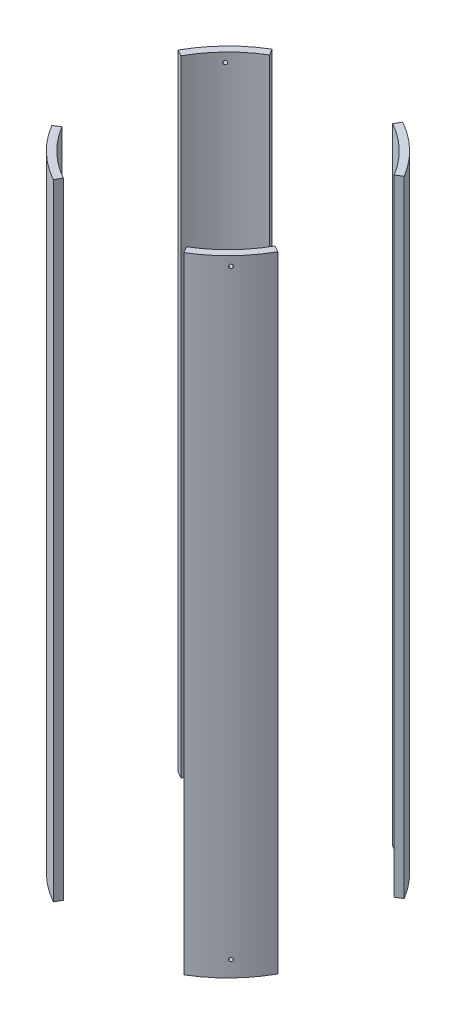
SolidWorks part; units mm, degrees
material "6061-T6 (SS)"
ref_plane "Front Plane" through (0, 0, 0) normal (0, 0, 1) x (1, 0, 0)
ref_plane "Top Plane" through (0, 0, 0) normal (0, 1, 0) x (1, 0, 0)
ref_plane "Right Plane" through (0, 0, 0) normal (1, 0, 0) x (0, 0, -1)
sketch "Sketch2" plane through (0, 0, 0) normal (0, 1, 0) x (1, 0, 0)
  circle A0 centre (0, 0) radius 88.9
  circle A1 centre (0, 0) radius 83.82
  dimension "D1" = 177.8
  dimension "D2" = 167.64
extrude "Boss-Extrude1" add sketch "Sketch2" along normal mid plane 432.943
sketch "Sketch3" plane through (0, 0, 0) normal (0, 1, 0) x (1, 0, 0)
  line L0 (0, 0) -> (169.6618, 101.6776)
  line L1 (-58.1167, 96.9749) -> (0, 0)
  line L2 (0, 0) -> (53.9, 96.9749)
  line L3 (53.9, 96.9749) -> (-58.1167, 96.9749)
  line L4 (0, 0) -> (70.9917, -118.4586)
  line L5 (70.9917, -118.4586) -> (-65.8409, -118.4586)
  line L6 (-65.8409, -118.4586) -> (0, 0)
  line L7 (169.6618, 101.6776) -> (169.6618, -94.3004)
  line L8 (169.6618, -94.3004) -> (0, 0)
  line L9 (0, 0) -> (-123.7413, 68.7771)
  line L10 (-123.7413, 68.7771) -> (-123.7413, -74.1577)
  line L11 (-123.7413, -74.1577) -> (0, 0)
  dimension "D1" = 60
  dimension "D2" = 60
  dimension "D3" = 60
  dimension "D4" = 60
  dimension "D5" = 30
  dimension "D6" = 30
extrude "Cut-Extrude1" cut sketch "Sketch3" against normal through all both and the other way through all contours L8 L7 L0 | L2 L3 L1 | L10 L11 L9 | L6 L5 L4
ref_plane "Bolt reference plane" through (-56.3092, 0, 58.1758) normal (0.6955, 0, -0.7185) x (-0.7185, 0, -0.6955)
sketch "Sketch5" plane through (-56.3092, 0, 58.1758) normal (0.6955, 0, -0.7185) x (-0.7185, 0, -0.6955)
  line L0 (-23.009, -216.4715) -> (23.009, -216.4715) construction
  circle A0 centre (-0.0228, 210.1215) radius 1.27
  circle A1 centre (-0.0228, -205.359) radius 1.27
  dimension "D1" = 2.54
  dimension "D4" = 11.1125
  dimension "D2" = 21.717
  dimension "D3" = 6.35
extrude "Bolt holes" cut sketch "Sketch5" against normal through all
pattern_circular "Bolt pattern" count 4 over 360 about axis through (0, 216.4715, 0) along (0, 1, 0) of "Bolt holes"
equation "\"D1@Boss-Extrude1\"=3*12"
